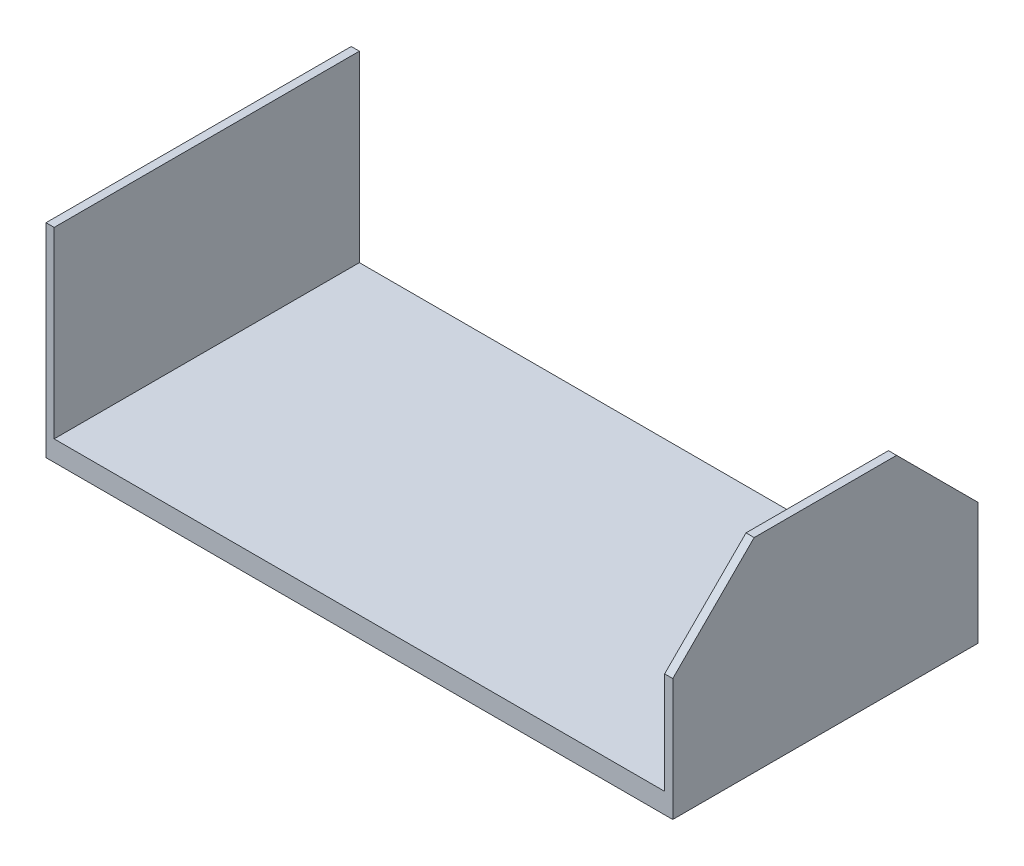
SolidWorks part; units mm, degrees
material "ABS"
ref_plane "Front Plane" through (0, 0, 0) normal (0, 0, 1) x (1, 0, 0)
ref_plane "Top Plane" through (0, 0, 0) normal (0, 1, 0) x (1, 0, 0)
ref_plane "Right Plane" through (0, 0, 0) normal (1, 0, 0) x (0, 0, -1)
sketch "Sketch1" plane through (0, 0, 0) normal (0, 1, 0) x (1, 0, 0)
  line L1 (75, 37.5) -> (-75, 37.5)
  line L2 (75, 37.5) -> (75, -37.5)
  line L3 (75, -37.5) -> (-75, -37.5)
  line L4 (-75, 37.5) -> (-75, -37.5)
  line L5 (75, 37.5) -> (-75, -37.5) construction
  line L6 (75, -37.5) -> (-75, 37.5) construction
  point P0 (0, 0)
  dimension "D1" = 75
  dimension "D2" = 150
extrude "Boss-Extrude1" add sketch "Sketch1" along normal blind 5
sketch "Sketch2" plane through (-75, 0, 0) normal (-1, 0, 0) x (0, 0, 1)
  line L1 (-37.5, 0) -> (37.5, 0)
  line L2 (-37.5, 0) -> (-37.5, 50)
  line L3 (-37.5, 50) -> (37.5, 50)
  line L4 (37.5, 0) -> (37.5, 50)
  line L6 (-37.5, 5) -> (37.5, 5) construction
  dimension "D1" = 45
extrude "Boss-Extrude2" add sketch "Sketch2" along normal blind 2
mirror "Mirror1" about plane through (0, 0, 0) normal (1, 0, 0) of "Boss-Extrude2"
chamfer "Chamfer1" distance 20 angle 45 2 edges at (76, 50, 37.5) (76, 50, -37.5)
